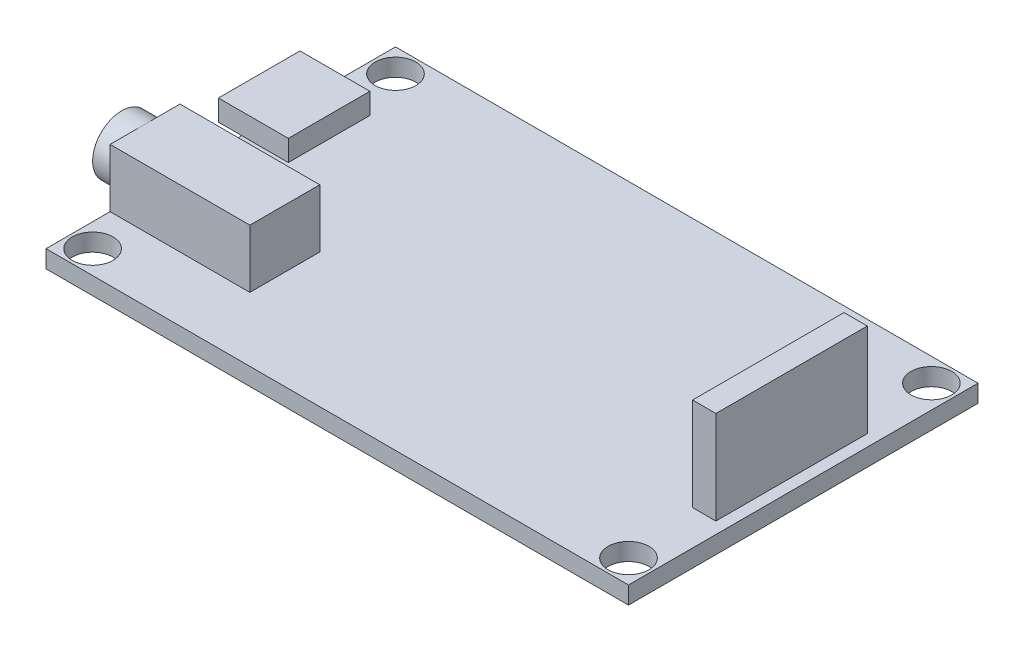
SolidWorks part; units mm, degrees
ref_plane "Front" through (0, 0, 0) normal (0, 0, 1) x (1, 0, 0)
ref_plane "Top" through (0, 0, 0) normal (0, 1, 0) x (1, 0, 0)
ref_plane "Right" through (0, 0, 0) normal (1, 0, 0) x (0, 0, -1)
sketch "Sketch1" plane through (0, 0, 0) normal (0, 1, 0) x (1, 0, 0)
  line L1 (0, 0) -> (50, 0)
  line L2 (0, 0) -> (0, -30)
  line L3 (0, -30) -> (50, -30)
  line L4 (50, 0) -> (50, -30)
  dimension "D1" = 50
  dimension "D2" = 30
extrude "Boss-Extrude1" add sketch "Sketch1" along normal blind 1.5
sketch "Sketch2" plane through (0, 1.5, 0) normal (0, 1, 0) x (1, 0, 0)
  line L0 (50, -30) -> (50, 0) construction
  line L1 (0, -30) -> (50, -30) construction
  line L2 (50, 0) -> (0, 0) construction
  line L3 (0, 0) -> (0, -30) construction
  circle A0 centre (48, -28) radius 1.75
  circle A1 centre (48, -2) radius 1.75
  circle A2 centre (2, -2) radius 1.75
  circle A3 centre (2, -28) radius 1.75
  point P10 (0, 0)
  dimension "D1" = 3.5
  dimension "D2" = 3.5
  dimension "D3" = 3.5
  dimension "D4" = 3.5
  dimension "D5" = 2
  dimension "D6" = 2
  dimension "D7" = 2
  dimension "D8" = 2
  dimension "D9" = 2
  dimension "D10" = 2
  dimension "D11" = 2
  dimension "D12" = 2
extrude "Cut-Extrude1" cut sketch "Sketch2" against normal through all
sketch "Sketch3" plane through (0, 1.5, 0) normal (0, 1, 0) x (1, 0, 0)
  line L0 (50, -30) -> (50, 0) construction
  line L1 (47, -8.5) -> (49, -8.5)
  line L2 (47, -8.5) -> (47, -21.5)
  line L3 (47, -21.5) -> (49, -21.5)
  line L4 (49, -8.5) -> (49, -21.5)
  line L5 (0, -30) -> (50, -30) construction
  point P8 (49, -15)
  dimension "D1" = 1
  dimension "D2" = 15
  dimension "D3" = 2
  dimension "D4" = 13
extrude "Boss-Extrude2" add sketch "Sketch3" along normal blind 8
sketch "Sketch4" plane through (0, 1.5, 0) normal (0, 1, 0) x (1, 0, 0)
  line L0 (0, 0) -> (0, -30) construction
  line L1 (0, -24.5) -> (12, -24.5)
  line L2 (0, -24.5) -> (0, -18.5)
  line L3 (0, -18.5) -> (12, -18.5)
  line L4 (12, -24.5) -> (12, -18.5)
  line L5 (0, -30) -> (50, -30) construction
  dimension "D1" = 5.5
  dimension "D2" = 6
  dimension "D3" = 12
extrude "Boss-Extrude3" add sketch "Sketch4" along normal blind 5
sketch "Sketch5" plane through (0, 0, 0) normal (-1, 0, 0) x (0, 0, 1)
  line L0 (18.5, 6.5) -> (24.5, 6.5) construction
  line L1 (18.5, 6.5) -> (18.5, 1.5) construction
  circle A0 centre (21.5, 4) radius 2.5
  point P6 (18.5, 4)
  dimension "D3" = 5
  dimension "D1" = 2.5
  dimension "D2" = 3
extrude "Boss-Extrude4" add sketch "Sketch5" along normal blind 2
sketch "Sketch6" plane through (0, 1.5, 0) normal (0, 1, 0) x (1, 0, 0)
  line L0 (50, 0) -> (0, 0) construction
  line L1 (-2, -13.2) -> (4, -13.2)
  line L2 (-2, -13.2) -> (-2, -6.2)
  line L3 (-2, -6.2) -> (4, -6.2)
  line L4 (4, -13.2) -> (4, -6.2)
  line L5 (0, 0) -> (0, -18.5) construction
  dimension "D1" = 6.2
  dimension "D2" = 7
  dimension "D3" = 6
  dimension "D4" = 2
extrude "Boss-Extrude5" add sketch "Sketch6" along normal blind 1.8
equation "\"dac_l\"=50"
equation "\"D1@Sketch1\"=\"dac_l\""
equation "\"dac_w\"=30"
equation "\"D2@Sketch1\"=\"dac_w\""
equation "\"h_r\"=3.5"
equation "\"D1@Sketch2\"=\"h_r\""
equation "\"D2@Sketch2\"=\"h_r\""
equation "\"D3@Sketch2\"=\"h_r\""
equation "\"D4@Sketch2\"=\"h_r\""
equation "\"h_dis\"=2"
equation "\"D5@Sketch2\"=\"h_dis\""
equation "\"D6@Sketch2\"=\"h_dis\""
equation "\"D7@Sketch2\"=\"h_dis\""
equation "\"D8@Sketch2\"=\"h_dis\""
equation "\"D9@Sketch2\"=\"h_dis\""
equation "\"D10@Sketch2\"=\"h_dis\""
equation "\"D11@Sketch2\"=\"h_dis\""
equation "\"D12@Sketch2\"=\"h_dis\""
equation "\"D2@Sketch3\"=\"dac_w\"/2"
